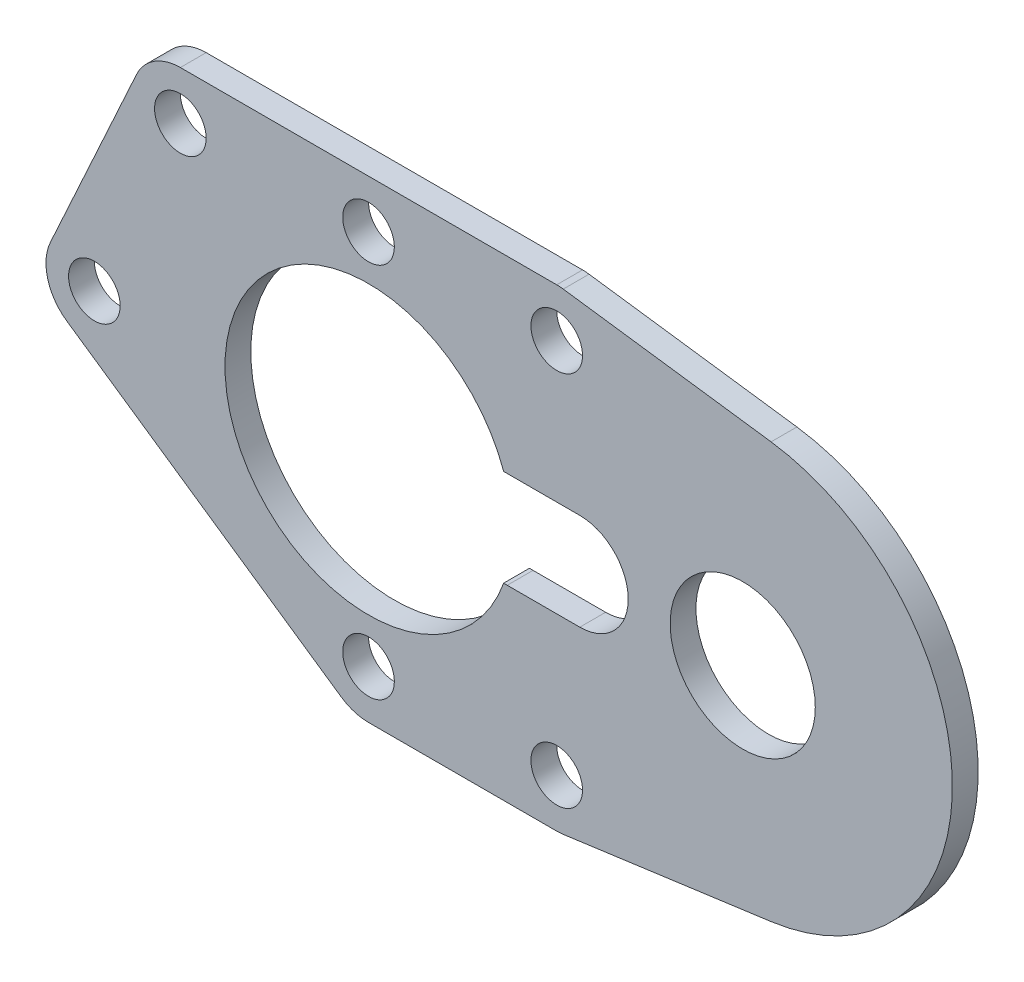
SolidWorks part; units mm, degrees
ref_plane "Front" through (0, 0, 0) normal (0, 0, 1) x (1, 0, 0)
ref_plane "Top" through (0, 0, 0) normal (0, 1, 0) x (1, 0, 0)
ref_plane "Right" through (0, 0, 0) normal (1, 0, 0) x (0, 0, -1)
sketch "Sketch1" plane through (0, 0, 0) normal (0, 0, 1) x (1, 0, 0)
  line L9 (12.0731, 14.6397) -> (24.9585, 12.8805)
  line L15 (12.0731, -14.6397) -> (24.9585, -12.8805)
  line L16 (11.6673, 14.6673) -> (-11.6673, 14.6673)
  line L17 (11.6673, -14.6673) -> (0, -14.6673)
  line L18 (-14.3958, 12.9144) -> (-19.7285, 1.2471)
  line L19 (-18.6976, -2.4735) -> (-1.6976, -14.1408)
  circle A17 centre (0, 0) radius 3
  circle A18 centre (23.2, 0) radius 4.5
  circle A19 centre (8.6, 0) radius 3
  circle A24 centre (-17, 0) radius 1.6
  arc A26 (12.0731, 14.6397) -> (11.6673, 14.6673) centre (11.6673, 11.6673) ccw
  arc A28 (-11.6673, 14.6673) -> (-14.3958, 12.9144) centre (-11.6673, 11.6673) ccw
  arc A29 (11.6673, -14.6673) -> (12.0731, -14.6397) centre (11.6673, -11.6673) ccw
  arc A30 (-1.6976, -14.1408) -> (0, -14.6673) centre (0, -11.6673) ccw
  arc A31 (-19.7285, 1.2471) -> (-18.6976, -2.4735) centre (-17, 0) ccw
  circle A32 centre (0, -11.6673) radius 1.6
  circle A33 centre (11.6673, -11.6673) radius 1.6
  circle A34 centre (-11.6673, 11.6673) radius 1.6
  circle A35 centre (0, 11.6673) radius 1.6
  circle A36 centre (11.6673, 11.6673) radius 1.6
  arc A37 (24.9585, -12.8805) -> (24.9585, 12.8805) centre (23.2, 0) ccw
extrude "Boss-Extrude3" add sketch "Sketch1" along normal blind 1.6
sketch "Sketch2" plane through (0, 0, 1.6) normal (0, 0, 1) x (1, 0, 0)
  line L1 (8.6, 3) -> (13.1, 3)
  line L3 (13.1, -3) -> (8.6, -3)
  arc A1 (13.1, -3) -> (13.1, 3) centre (13.1, 0) ccw
  circle A2 centre (8.6, 0) radius 3 construction
  arc A3 (8.6, 3) -> (8.6, -3) centre (8.6, 0) ccw
extrude "Cut-Extrude1" cut sketch "Sketch2" against normal blind 10
sketch "Sketch3" plane through (0, 0, 1.6) normal (0, 0, 1) x (1, 0, 0)
  circle A0 centre (0, 0) radius 8.9
extrude "Cut-Extrude2" cut sketch "Sketch3" against normal blind 30
